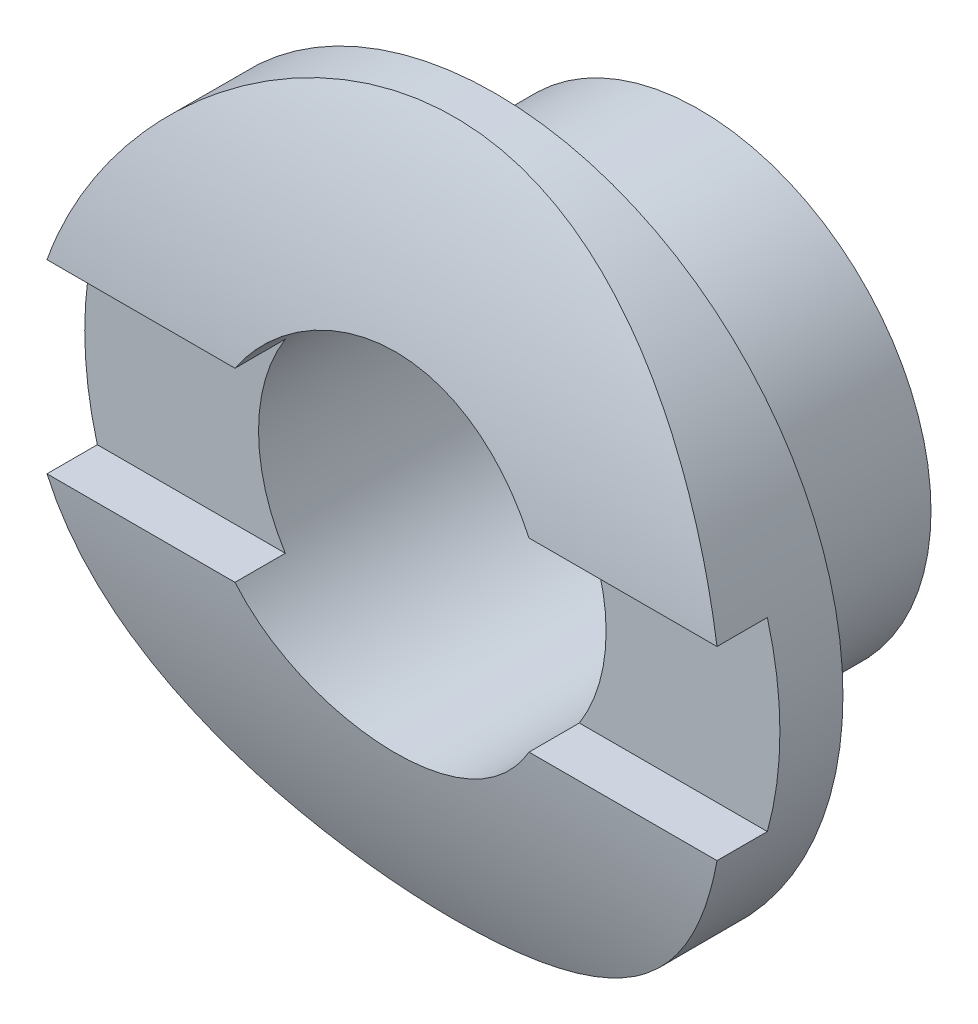
SolidWorks part; units mm, degrees
ref_plane "Front Plane" through (0, 0, 0) normal (0, 0, 1) x (1, 0, 0)
ref_plane "Top Plane" through (0, 0, 0) normal (0, 1, 0) x (1, 0, 0)
ref_plane "Right Plane" through (0, 0, 0) normal (1, 0, 0) x (0, 0, -1)
sketch "Sketch1" plane through (0, 0, 0) normal (0, 0, 1) x (1, 0, 0)
  circle A0 centre (0, 0) radius 3.175
  circle A1 centre (0, 0) radius 2.3813
  dimension "D1" = 4.7625
  dimension "D3" = 6.35
extrude "Boss-Extrude1" add sketch "Sketch1" along normal blind 2.794 contours A0
sketch "Sketch2" plane through (0, 0, 2.794) normal (0, 0, 1) x (1, 0, 0)
  circle A0 centre (0, 0) radius 4.7625
  circle A1 centre (0, 0) radius 2.3813
  dimension "D1" = 9.525
  dimension "D2" = 4.7625
extrude "Boss-Extrude2" add sketch "Sketch2" along normal blind 1.6256
sketch "Sketch3" plane through (0, 0, 0) normal (1, 0, 0) x (0, 0, -1)
  line L0 (-4.4196, 0) -> (6.7564, 0) construction
  line L1 (-4.4196, 4.7625) -> (-4.4196, -4.7625) construction
  circle A0 centre (6.7564, 0) radius 11.176
  circle A1 centre (6.7564, 0) radius 22.3612
  dimension "D1" = 11.176
extrude "Cut-Extrude1" cut sketch "Sketch3" against normal through all and the other way through all
sketch "Sketch4" plane through (0, 0, 0) normal (1, 0, 0) x (0, 0, -1)
  line L1 (-4.4196, 1.27) -> (-3.6576, 1.27)
  line L2 (-4.4196, 1.27) -> (-4.4196, -1.27)
  line L3 (-4.4196, -1.27) -> (-3.6576, -1.27)
  line L4 (-3.6576, 1.27) -> (-3.6576, -1.27)
  arc A0 (-4.163, 2.3813) -> (-4.163, -2.3813) centre (6.7564, 0) ccw construction
  point P7 (-3.6576, 0)
  dimension "D1" = 0.762
  dimension "D2" = 2.54
extrude "Cut-Extrude2" cut sketch "Sketch4" against normal through all both and the other way through all
